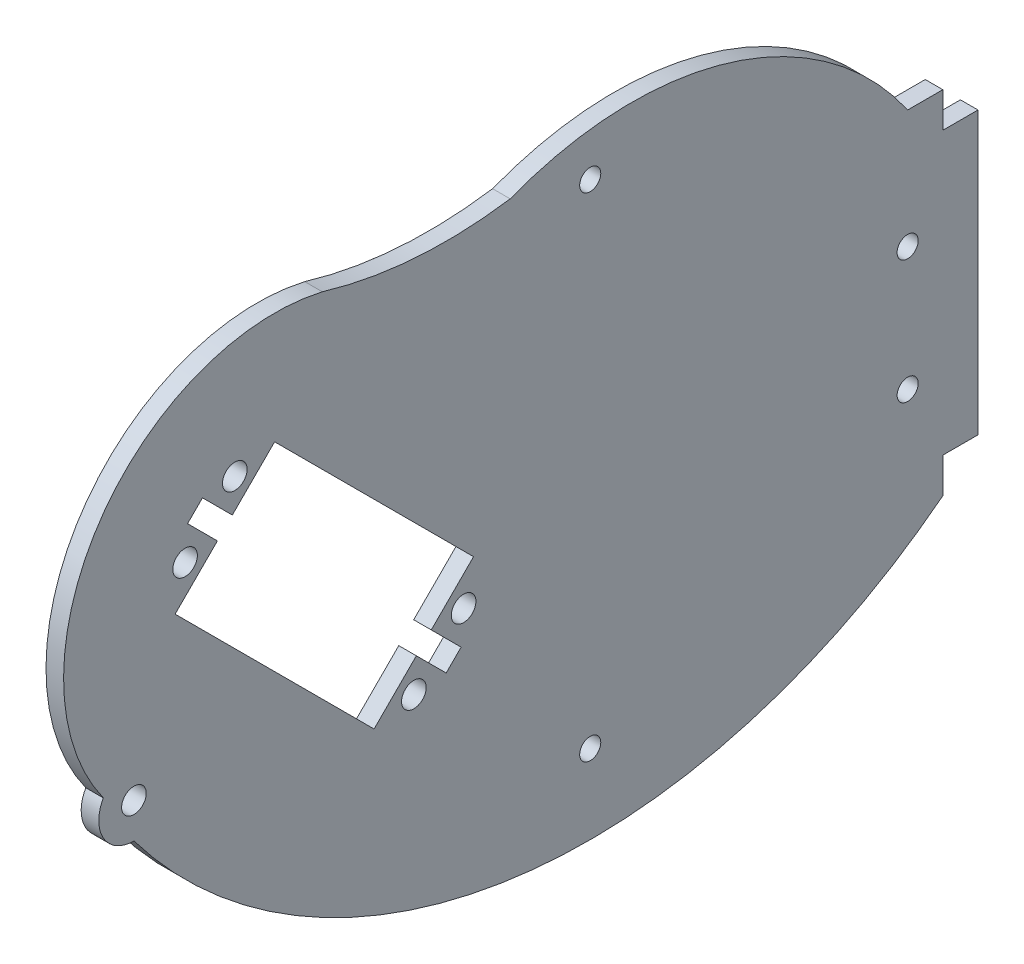
SolidWorks part; units mm, degrees
ref_plane "Alzado" through (0, 0, 0) normal (0, 0, 1) x (1, 0, 0)
ref_plane "Planta" through (0, 0, 0) normal (0, 1, 0) x (1, 0, 0)
ref_plane "Vista lateral" through (0, 0, 0) normal (1, 0, 0) x (0, 0, -1)
sketch "Croquis1" plane through (0, 0, 0) normal (1, 0, 0) x (0, 0, -1)
  line L0 (0, 0) -> (-7.0711, 7.0711) construction
  line L1 (-7.0711, 7.0711) -> (-14.1421, 0) construction
  line L2 (-14.1421, 0) -> (14.1421, -28.2843)
  line L3 (14.1421, -28.2843) -> (20.1507, -22.2757)
  line L4 (20.1507, -22.2757) -> (24.3934, -26.5183)
  line L5 (24.3934, -26.5183) -> (26.5165, -24.3952)
  line L6 (26.5165, -24.3952) -> (22.2739, -20.1525)
  line L7 (22.2739, -20.1525) -> (28.2843, -14.1421)
  line L8 (28.2843, -14.1421) -> (0, 14.1421)
  line L9 (0, 14.1421) -> (-6.0104, 8.1317)
  line L10 (-6.0104, 8.1317) -> (-10.253, 12.3744)
  line L11 (-10.253, 12.3744) -> (-12.3744, 10.253)
  line L12 (-12.3744, 10.253) -> (-8.1317, 6.0104)
  line L13 (-8.1317, 6.0104) -> (-14.1421, 0)
  line L14 (-10.253, 8.1317) -> (-12.7301, 5.6547) construction
  line L15 (-12.7301, 5.6547) -> (-10.6088, 3.5334) construction
  line L16 (-8.1317, 10.253) -> (-5.6585, 12.7263) construction
  line L17 (-5.6585, 12.7263) -> (-3.5372, 10.605) construction
  line L18 (24.3952, -22.2739) -> (26.8701, -19.799) construction
  line L19 (26.8701, -19.799) -> (24.7487, -17.6777) construction
  line L20 (22.272, -24.397) -> (19.7972, -26.8719) construction
  line L21 (19.7972, -26.8719) -> (17.6758, -24.7506) construction
  line L22 (0, 0) -> (100, 0) construction
  line L24 (95, 10) -> (90, 10)
  line L34 (95, -40) -> (95, -35) construction
  line L39 (95, -40) -> (95, -35)
  line L40 (95, -35) -> (100, -35)
  line L41 (100, -35) -> (100, 5)
  line L42 (100, 5) -> (95, 5)
  line L43 (95, 10) -> (95, 5)
  circle A0 centre (-12.7301, 5.6547) radius 1.75
  circle A1 centre (-5.6585, 12.7263) radius 1.75
  circle A2 centre (26.8701, -19.799) radius 1.75
  circle A3 centre (19.7972, -26.8719) radius 1.75
  circle A4 centre (-20, -20) radius 1.75
  arc A5 (6.7853, 29.2226) -> (33.4941, 27.3116) centre (24.3979, 87.7831) ccw
  arc A6 (-24.3465, -17.5285) -> (-20, -25) centre (-20, -20) ccw
  arc A7 (-20, -25) -> (95, -40) centre (44.8712, 24.0125) ccw
  arc A8 (33.4941, 27.3116) -> (90, 10) centre (50.7819, -17.1348) cw
  circle A9 centre (90, -6.8212) radius 1.5
  arc A10 (6.7853, 29.2226) -> (-24.3465, -17.5285) centre (0, 0) ccw
  circle A11 centre (90, -24.3952) radius 1.5
  circle A12 centre (44.8712, -46.0488) radius 1.5
  circle A13 centre (44.8712, 24.0125) radius 1.5
  dimension "D2" = 5
  dimension "D1" = 5
  dimension "D3" = 40
  dimension "D4" = 5
  dimension "D6" = 100
extrude "Saliente-Extruir1" add sketch "Croquis1" along normal blind 2.5
